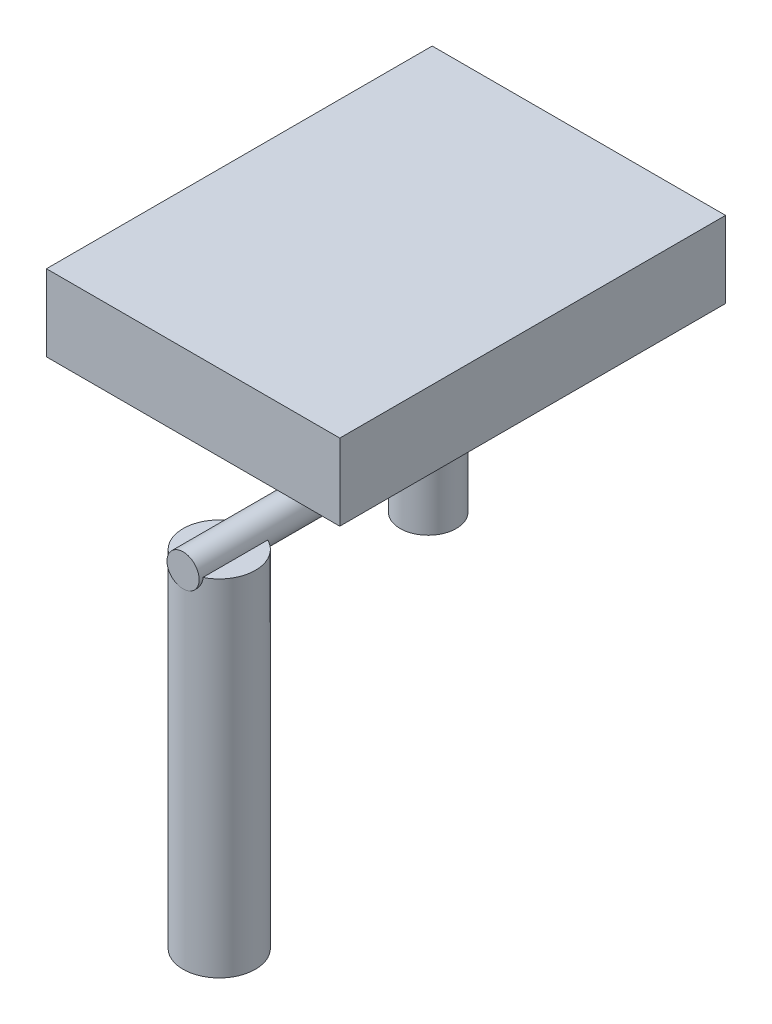
SolidWorks part; units mm, degrees
ref_plane "Plan de face" through (0, 0, 0) normal (0, 0, 1) x (1, 0, 0)
ref_plane "Plan de dessus" through (0, 0, 0) normal (0, 1, 0) x (1, 0, 0)
ref_plane "Plan de droite" through (0, 0, 0) normal (1, 0, 0) x (0, 0, -1)
sketch "Esquisse1" plane through (0, 0, 0) normal (0, 0, 1) x (1, 0, 0)
  line L1 (-79.1518, 36.8928) -> (285.8482, 36.8928)
  line L2 (-79.1518, 36.8928) -> (-79.1518, -58.1072)
  line L3 (-79.1518, -58.1072) -> (285.8482, -58.1072)
  line L4 (285.8482, 36.8928) -> (285.8482, -58.1072)
  dimension "D1" = 365
  dimension "D2" = 95
extrude "Boss.-Extru.1" add sketch "Esquisse1" along normal blind 480
sketch "Esquisse3" plane through (0, -58.1072, 0) normal (0, -1, 0) x (1, 0, 0)
  line L0 (-79.1518, 0) -> (285.8482, 0) construction
  line L1 (-79.1518, 480) -> (-79.1518, 0) construction
  circle A0 centre (90.8482, 175) radius 35
  dimension "D1" = 70
  dimension "D2" = 175
  dimension "D3" = 170
extrude "Boss.-Extru.2" add sketch "Esquisse3" along normal blind 235
sketch "Esquisse4" plane through (0, 0, 480) normal (0, 0, 1) x (1, 0, 0)
  line L0 (55.8482, -293.1072) -> (125.8482, -293.1072) construction
  line L3 (90.8482, -293.1072) -> (90.8482, -78.2123) construction
  circle A0 centre (90.8482, -203.1072) radius 20
  dimension "D1" = 40
  dimension "D2" = 90
extrude "Boss.-Extru.3" add sketch "Esquisse4" against normal up to next
sketch "Esquisse5" plane through (0, -58.1072, 0) normal (0, -1, 0) x (1, 0, 0)
  line L0 (90.8482, 480) -> (90.8482, 475.387) construction
  line L1 (110.8482, 480) -> (70.8482, 480) construction
  line L2 (90.8482, 475.387) -> (90.8482, 431.8221) construction
  line L3 (90.8482, 431.8221) -> (90.8482, 408.0961) construction
  line L4 (90.8482, 408.0961) -> (90.8482, 431.8221) construction
  line L5 (90.8482, 431.8221) -> (90.8482, 480) construction
  circle A0 centre (90.8482, 435) radius 45
  dimension "D1" = 90
  dimension "D2" = 45
extrude "Boss.-Extru.4" add sketch "Esquisse5" along normal blind 430 from offset 145 separate body
sketch "Esquisse6" plane through (0, -58.1072, 0) normal (0, -1, 0) x (1, 0, 0)
  line L0 (-79.1518, 480) -> (-79.1518, 0) construction
  line L1 (-79.1518, 210) -> (125.8482, 210)
  line L2 (-79.1518, 210) -> (-79.1518, 140)
  line L3 (-79.1518, 140) -> (125.8482, 140)
  line L4 (125.8482, 210) -> (125.8482, 140)
  circle A1 centre (90.8482, 175) radius 35 construction
  arc A2 (110.8482, 203.7228) -> (70.8482, 203.7228) centre (90.8482, 175) ccw construction
extrude "Boss.-Extru.5" add sketch "Esquisse6" along normal blind 55
sketch "Esquisse7" plane through (0, -58.1072, 0) normal (0, -1, 0) x (1, 0, 0)
  circle A0 centre (90.8482, 175) radius 60
  dimension "D1" = 120
extrude "Boss.-Extru.6" add sketch "Esquisse7" along normal blind 50
equation "\"LargeurPlacard\"=160+70+135"
equation "\"D1@Esquisse1\"=\"LargeurPlacard\""
equation "\"EpaisseurPlaque\"= 10"
equation "\"ProfondeurPlacard\"=580"
equation "\"DistanceAvantSyphon\"=240"
equation "\"DistanceAvantEvier\"=100"
equation "\"DiametreTuyau\"=90"
equation "\"HauteurTuyau\"=430"
equation "\"LargeurAeration\"=260"
equation "\"HauteurAeration\"=340"
equation "\"AerationSol\"=210"
equation "\"AerationAvant\"=270"
equation "\"ProfondeurCharniere\"=80"
equation "\"HauteurCharniere\"=60"
equation "\"LargeurCharniere\"=60"
equation "\"HauteurPlacard\"=650"
equation "\"HauteurEvier\"=\"HauteurPlacard\"-555"
equation "\"HauteurDroitEvier\"=\"HauteurPlacard\" -500"
equation "\"HauteurSolSyphon\"=320"
equation "\"DiametreSyphon\"=70"
equation "\"PositionSyphonCoteGauche\"=160"
equation "\"D2@Esquisse1\"=\"HauteurEvier\""
equation "\"D1@Boss.-Extru.1\"=\"ProfondeurPlacard\"-\"DistanceAvantEvier\""
equation "\"D1@Esquisse3\"=\"DiametreSyphon\""
equation "\"D2@Esquisse3\"=\"DistanceAvantSyphon\"+\"DiametreSyphon\"/2mm - \"DistanceAvantEvier\""
equation "\"D1@Boss.-Extru.2\"=555-\"HauteurSolSyphon\""
equation "\"D1@Esquisse4\"=40"
equation "\"D2@Esquisse4\"=\"HauteurTuyau\"-\"HauteurSolSyphon\"-20"
equation "\"D1@Esquisse5\"=\"DiametreTuyau\""
equation "\"D2@Esquisse5\"=\"DiametreTuyau\"/2"
equation "\"D1@Boss.-Extru.4\"=\"HauteurTuyau\""
equation "\"555mm-\"=0"
equation "\"D19@Boss.-Extru.4\"=465 - \"HauteurSolSyphon\""
equation "\"D1@Boss.-Extru.5\"=55"
equation "\"D1@Esquisse7\"=2*(\"PositionSyphonCoteGauche\"+\"DiametreSyphon\"/2-135)"
